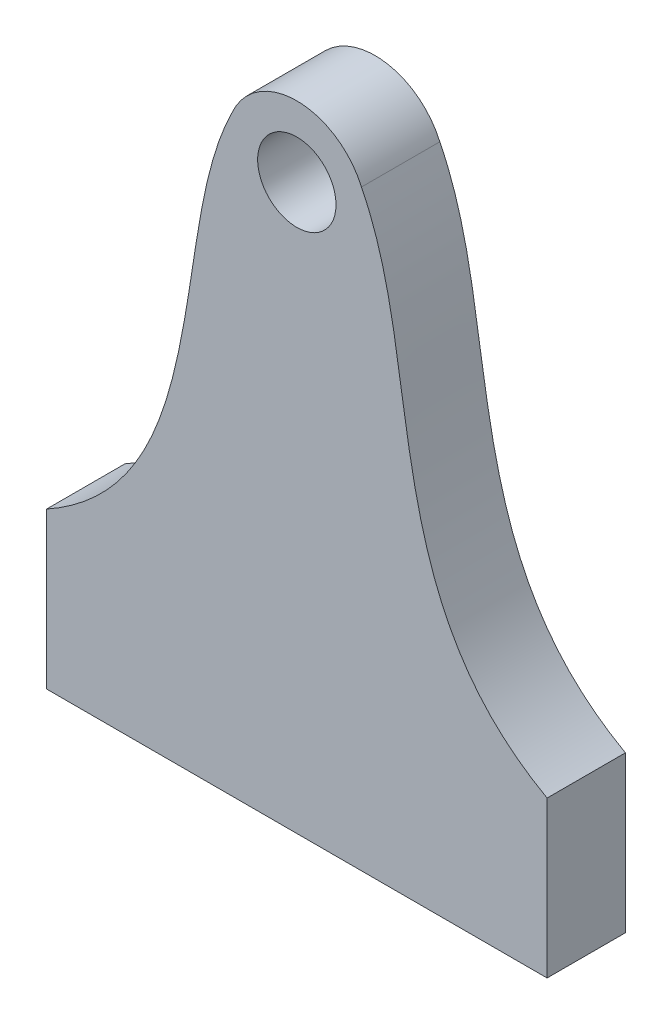
SolidWorks part; units mm, degrees
ref_plane "Front Plane" through (0, 0, 0) normal (0, 0, 1) x (1, 0, 0)
ref_plane "Top Plane" through (0, 0, 0) normal (0, 1, 0) x (1, 0, 0)
ref_plane "Right Plane" through (0, 0, 0) normal (1, 0, 0) x (0, 0, -1)
sketch "Sketch1" plane through (0, 0, 0) normal (0, 0, 1) x (1, 0, 0)
  line L0 (0, 0) -> (0, 45.72) construction
  line L1 (20.2849, 0) -> (20.2849, 12.6325)
  line L2 (20.2849, 0) -> (-20.2849, 0)
  line L5 (-20.2849, 0) -> (-20.2849, 12.6325)
  circle A0 centre (0, 45.72) radius 3.175
  arc A2 (5.2399, 48.0013) -> (-5.2399, 48.0013) centre (0, 45.72) ccw
  spline S0 degree 3 poles (-20.2849, 12.6325) (-11.3216, 17.627) (-9.1455, 30.7666) (-7.1272, 44.2326) (-5.2399, 48.0013) knots 0 0 0 0 0.567527 0.844926 0.844926 0.844926 0.844926
  spline S1 degree 3 poles (20.2849, 12.6325) (11.3216, 17.627) (9.1455, 30.7666) (7.1272, 44.2326) (5.2399, 48.0013) knots 0 0 0 0 0.567527 0.844926 0.844926 0.844926 0.844926
  dimension "D1" = 6.35
  dimension "D3" = 11.43
  dimension "D2" = 45.72
  dimension "D4" = 90
extrude "Boss-Extrude1" add sketch "Sketch1" along normal blind 6.35
